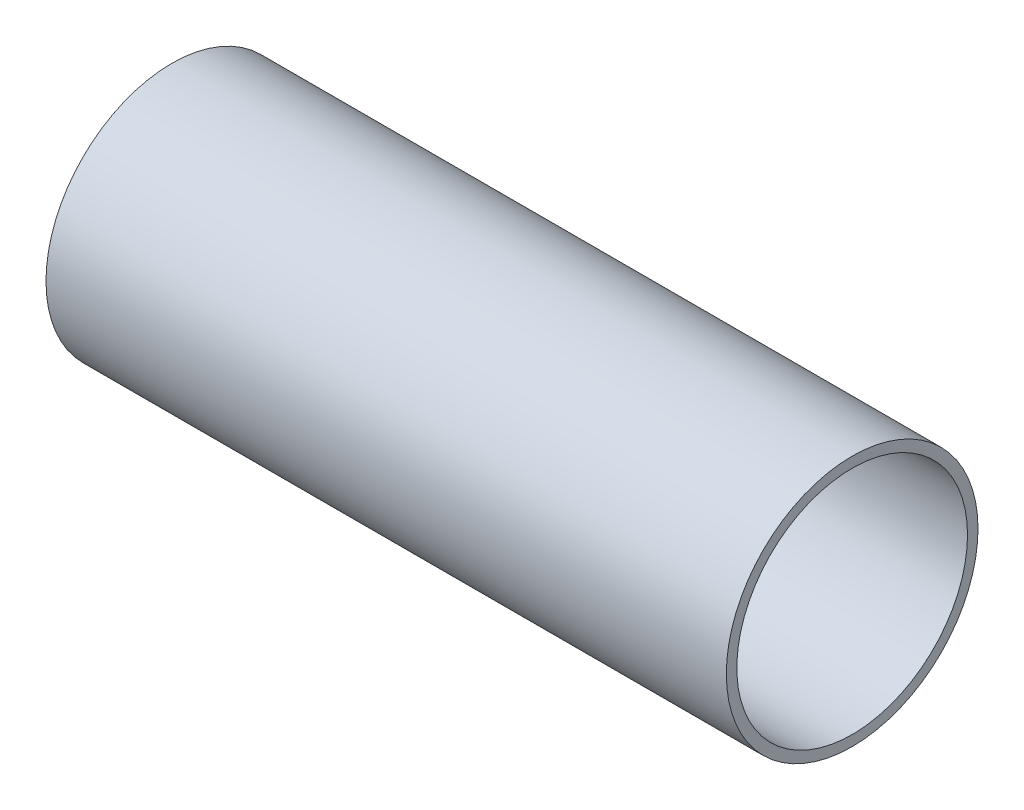
SolidWorks part; units mm, degrees
ref_plane "Front Plane" through (0, 0, 0) normal (0, 0, 1) x (1, 0, 0)
ref_plane "Top Plane" through (0, 0, 0) normal (0, 1, 0) x (1, 0, 0)
ref_plane "Right Plane" through (0, 0, 0) normal (1, 0, 0) x (0, 0, -1)
sketch "Sketch1" plane through (0, 0, 0) normal (1, 0, 0) x (0, 0, -1)
  circle A0 centre (0, 0) radius 69.85
  circle A1 centre (0, 0) radius 76.2
  dimension "D1" = 139.7
  dimension "D2" = 152.4
extrude "Boss-Extrude1" add sketch "Sketch1" along normal mid plane 412
